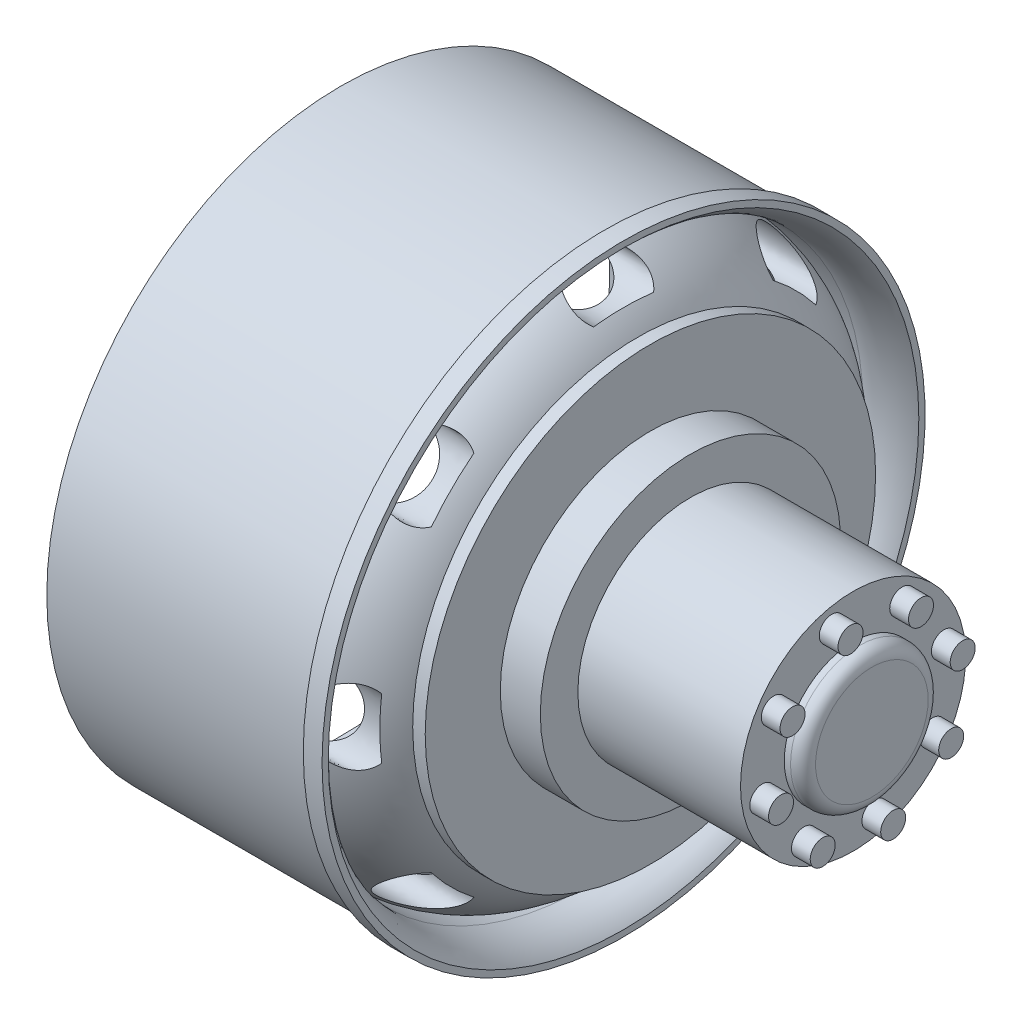
SolidWorks part; units mm, degrees
ref_plane "Front Plane" through (0, 0, 0) normal (0, 0, 1) x (1, 0, 0)
ref_plane "Top Plane" through (0, 0, 0) normal (0, 1, 0) x (1, 0, 0)
ref_plane "Right Plane" through (0, 0, 0) normal (1, 0, 0) x (0, 0, -1)
sketch "Sketch1" plane through (0, 0, 0) normal (0, 0, 1) x (1, 0, 0)
  line L0 (-25, 0) -> (25, 0) construction
  line L1 (0, 36.6286) -> (0, -30.4082) construction
  line L2 (-10, 23.5) -> (11.1, 23.5)
  line L3 (11.1, 23.5) -> (11.1, 24.1)
  line L4 (11.1, 24.1) -> (12.6, 24.1)
  line L5 (12.6, 24.1) -> (12.6, 23.6)
  line L9 (-10, 21.5) -> (-10, 23.5)
  line L27 (9.4257, 22.3) -> (6, 22.3)
  line L43 (-10, 21.5) -> (3.8066, 21.5)
  line L44 (6, 20.3) -> (3.8066, 20.3)
  line L45 (3.8066, 20.3) -> (3.8066, 21.5)
  line L47 (12.542, 16) -> (12.542, 8.4837)
  line L48 (-10, 21.5) -> (11.1, 21.5) construction
  line L49 (15.7458, 18) -> (15.7458, 0) construction
  line L51 (13.7458, 16) -> (13.7458, 0) construction
  line L54 (18.9458, 9) -> (30.9458, 9)
  line L55 (12.542, 16) -> (13.7458, 16) construction
  line L57 (12.542, 8.4837) -> (12.542, 0)
  line L58 (12.542, 0) -> (30.9458, 0)
  line L59 (30.9458, 0) -> (30.9458, 9)
  line L66 (13.7458, 18) -> (14.7458, 18)
  line L67 (13.7458, 18) -> (15.7458, 18) construction
  line L68 (14.7458, 18) -> (14.7458, 12)
  line L70 (14.7458, 12) -> (17.9458, 12)
  line L71 (17.9458, 12) -> (17.9458, 9)
  line L72 (17.9458, 9) -> (18.9458, 9)
  arc A1 (12.6, 23.6) -> (9.4257, 22.3) centre (9.6236, 26.3422) cw
  arc A4 (6, 22.3) -> (13.7458, 18) centre (6, 13.1735) cw
  arc A5 (6, 20.3) -> (12.542, 16) centre (6, 13.1735) cw
  point P13 (12.9671, 14)
  point P21 (16.5518, 14)
  point P24 (12.9671, 11)
  point P27 (16.5518, 11)
  dimension "D1" = 50
  dimension "D2" = 25
  dimension "D3" = 1
  dimension "D4" = 21.1
  dimension "D5" = 48.2
  dimension "D6" = 0.5
  dimension "D7" = 1.5
  dimension "D8" = 18
  dimension "D9" = 2
  dimension "D10" = 2
  dimension "D11" = 47
  dimension "D12" = 3.2
  dimension "D13" = 12
  dimension "D14" = 2.2038
revolve "Revolve1" add sketch "Sketch1" angle 360 about L0
sketch "Sketch3" plane through (12.6, 0, 0) normal (1, 0, 0) x (0, 0, -1)
  line L0 (0, 23.6) -> (0, -24.1) construction
  line L1 (-24.1, 0) -> (24.1, 0) construction
  circle A0 centre (0, 0) radius 23.6 construction
  circle A1 centre (0, 0) radius 24.1 construction
  ellipse E0 centre (0, 20.3231) end of major axis (3, 20.3231) minor radius 1.6667
  dimension "D1" = 6
extrude "Cut-Extrude2" cut sketch "Sketch3" against normal up to surface (8.7934 mm away) up to face at (3.8066, 0, 20.3)
pattern_circular "CirPattern1" count 8 over 360 of "Cut-Extrude2"
sketch "Sketch4" plane through (30.9458, 0, 0) normal (1, 0, 0) x (0, 0, -1)
  circle A0 centre (-1.7058, 7.26) radius 1
  circle A1 centre (3.9274, 6.3398) radius 1
  circle A2 centre (7.26, 1.7058) radius 1
  circle A3 centre (6.3398, -3.9274) radius 1
  circle A4 centre (1.7058, -7.26) radius 1
  circle A5 centre (-3.9274, -6.3398) radius 1
  circle A6 centre (-7.26, -1.7058) radius 1
  circle A7 centre (-6.3398, 3.9274) radius 1
  circle A8 centre (0, 0) radius 5.5
  point P4 (-1.6752, 7.0457)
  point P19 (0, 0)
  point P21 (-1.7058, 7.26)
  dimension "D1" = 2
  dimension "D3" = 11
  dimension "D2" = 8
extrude "Boss-Extrude1" add sketch "Sketch4" along normal blind 1.5
fillet "Fillet1" radius 1 1 edges at (32.4458, 0, -5.5)
